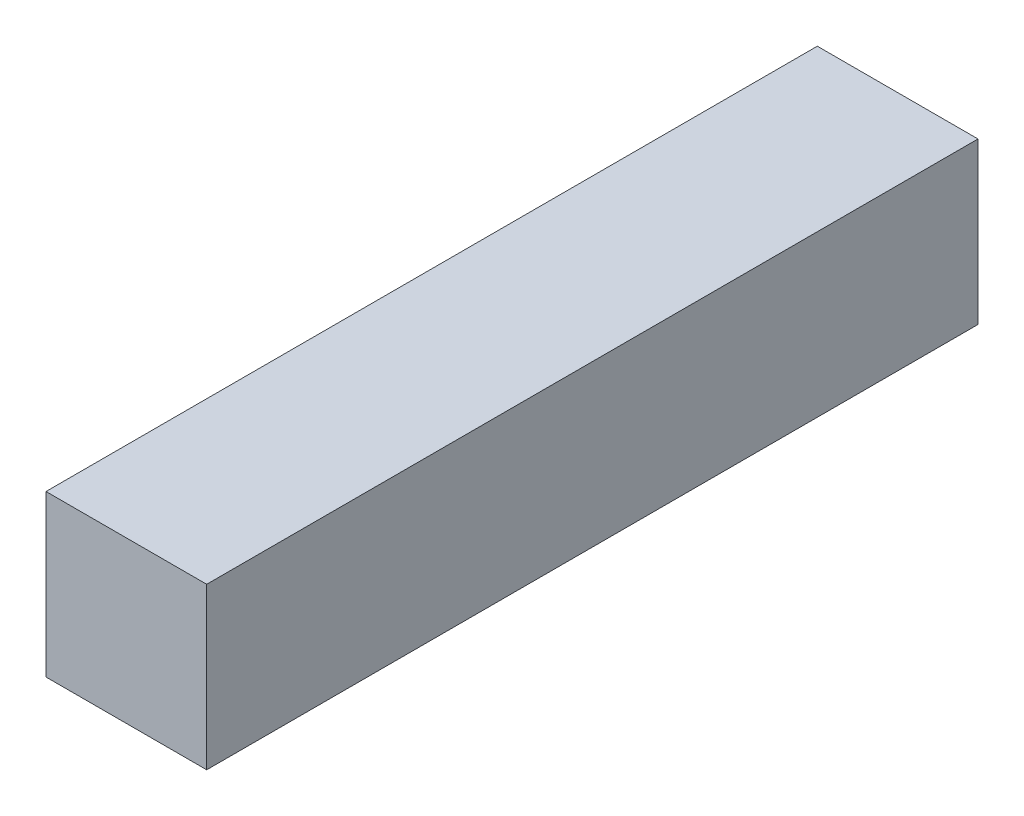
SolidWorks part; units mm, degrees
ref_plane "Front Plane" through (0, 0, 0) normal (0, 0, 1) x (1, 0, 0)
ref_plane "Top Plane" through (0, 0, 0) normal (0, 1, 0) x (1, 0, 0)
ref_plane "Right Plane" through (0, 0, 0) normal (1, 0, 0) x (0, 0, -1)
sketch "Sketch2" plane through (0, 0, 0) normal (0, 0, 1) x (1, 0, 0)
  line L1 (-61.5156, -40.6797) -> (1.9844, -40.6797)
  line L2 (-61.5156, -40.6797) -> (-61.5156, 22.8203)
  line L3 (-61.5156, 22.8203) -> (1.9844, 22.8203)
  line L4 (1.9844, -40.6797) -> (1.9844, 22.8203)
  line L5 (-61.5156, -40.6797) -> (1.9844, 22.8203) construction
  line L6 (-61.5156, 22.8203) -> (1.9844, -40.6797) construction
  point P0 (-29.7656, -8.9297)
  dimension "D1" = 63.5
  dimension "D2" = 63.5
extrude "Boss-Extrude1" add sketch "Sketch2" along normal blind 304.8
